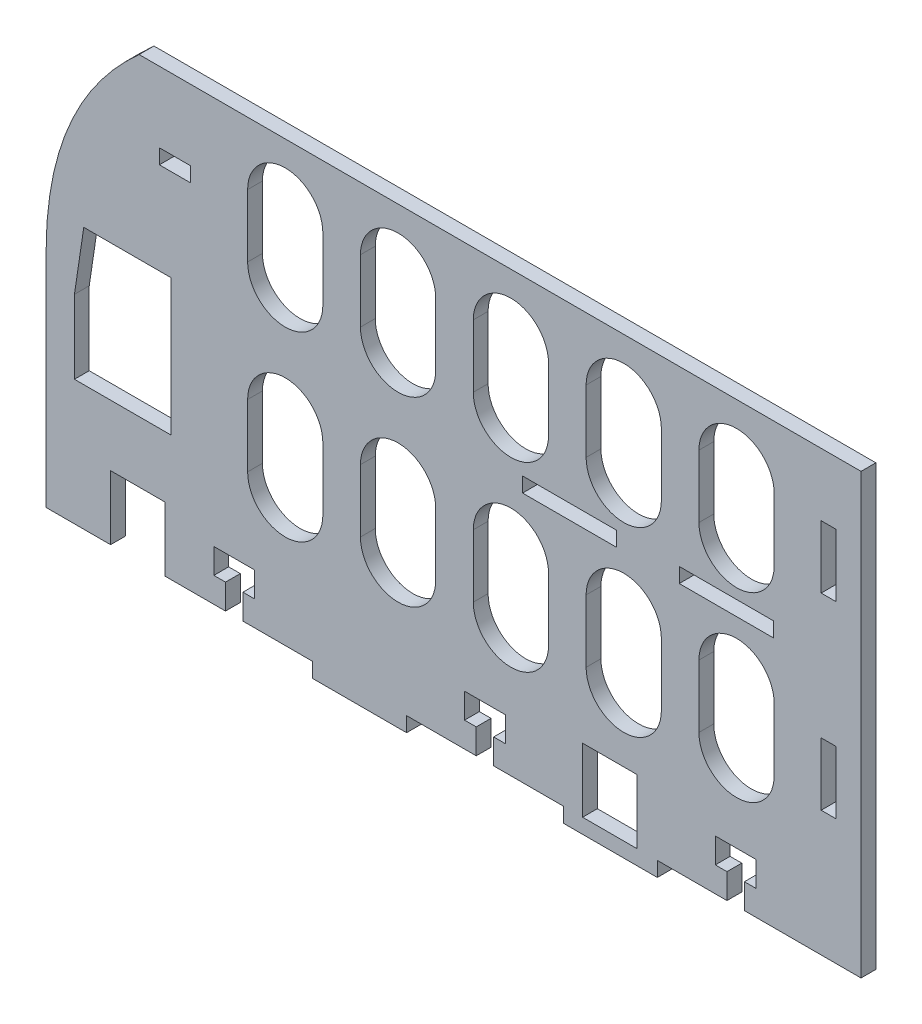
SolidWorks part; units mm, degrees
ref_plane "Front Plane" through (0, 0, 0) normal (0, 0, 1) x (1, 0, 0)
ref_plane "Top Plane" through (0, 0, 0) normal (0, 1, 0) x (1, 0, 0)
ref_plane "Right Plane" through (0, 0, 0) normal (1, 0, 0) x (0, 0, -1)
sketch "Sketch1" plane through (0, 0, 0) normal (0, 0, 1) x (1, 0, 0)
  line L0 (-76.2, -31.75) -> (-76.2, -10.2034) construction
  line L1 (2.72, 1.27) -> (-88.9648, 1.27) construction
  line L2 (50.8, 31.75) -> (50.8, -31.75)
  line L3 (-114.3, -31.75) -> (-101.25, -31.75)
  line L4 (25.58, 7.62) -> (25.58, -5.08) construction
  line L5 (-74.4347, -26.67) -> (-72.0725, -26.67)
  line L6 (-29.5275, -21.59) -> (-21.2725, -21.59)
  line L7 (-77.9653, -31.75) -> (-77.9653, -26.67)
  line L8 (-74.4347, -31.75) -> (-60.325, -31.75)
  line L9 (-74.4347, -31.75) -> (-74.4347, -26.67)
  line L10 (-80.3275, -26.67) -> (-77.9653, -26.67)
  line L11 (-80.3275, -26.67) -> (-80.3275, -21.59)
  line L12 (-80.3275, -21.59) -> (-72.0725, -21.59)
  line L13 (-72.0725, -26.67) -> (-72.0725, -21.59)
  line L14 (-21.2725, -26.67) -> (-21.2725, -21.59)
  line L15 (-23.6347, -26.67) -> (-21.2725, -26.67)
  line L16 (-29.5275, -26.67) -> (-27.1653, -26.67)
  line L17 (-27.1653, -31.75) -> (-27.1653, -26.67)
  line L18 (-23.6347, -31.75) -> (-23.6347, -26.67)
  line L19 (-29.5275, -26.67) -> (-29.5275, -21.59)
  line L20 (21.2725, -21.59) -> (29.5275, -21.59)
  line L21 (29.5275, -26.67) -> (29.5275, -21.59)
  line L22 (27.1653, -26.67) -> (29.5275, -26.67)
  line L23 (21.2725, -26.67) -> (23.6347, -26.67)
  line L24 (23.6347, -31.75) -> (23.6347, -26.67)
  line L25 (27.1653, -31.75) -> (27.1653, -26.67)
  line L26 (21.2725, -26.67) -> (21.2725, -21.59)
  line L27 (33.2, 7.62) -> (33.2, -5.08)
  line L28 (17.96, 7.62) -> (17.96, -5.08)
  line L29 (25.58, 1.27) -> (-66.1048, 1.27) construction
  line L30 (45.72, 31.75) -> (42.72, 31.75)
  line L31 (2.72, 7.62) -> (2.72, -5.08) construction
  line L32 (10.34, 7.62) -> (10.34, -5.08)
  line L33 (-4.9, 7.62) -> (-4.9, -5.08)
  line L34 (-23.6347, -31.75) -> (-9.525, -31.75)
  line L35 (27.1653, -31.75) -> (50.8, -31.75)
  line L36 (-114.3, -31.75) -> (-114.3, 12.7)
  line L37 (-20.14, 1.27) -> (-111.8248, 1.27) construction
  line L38 (-20.14, 7.62) -> (-20.14, -5.08) construction
  line L39 (-12.52, 7.62) -> (-12.52, -5.08)
  line L40 (45.72, -6.35) -> (42.72, -6.35)
  line L41 (45.72, 31.75) -> (45.72, 44.45)
  line L42 (9.525, -31.75) -> (23.6347, -31.75)
  line L43 (45.72, -6.35) -> (45.72, 6.35)
  line L44 (45.72, 6.35) -> (42.72, 6.35)
  line L45 (-60.325, -31.75) -> (-60.325, -34.75)
  line L46 (-60.325, -34.75) -> (-41.275, -34.75)
  line L47 (-41.275, -31.75) -> (-41.275, -34.75)
  line L48 (-50.8, -31.75) -> (-41.275, -34.75) construction
  line L49 (-60.325, -34.75) -> (-50.8, -31.75) construction
  line L50 (-41.275, -31.75) -> (-27.1653, -31.75)
  line L51 (-9.525, -31.75) -> (-9.525, -34.75)
  line L52 (-9.525, -34.75) -> (9.525, -34.75)
  line L53 (9.525, -31.75) -> (9.525, -34.75)
  line L54 (0, -31.75) -> (9.525, -34.75) construction
  line L55 (-9.525, -34.75) -> (0, -31.75) construction
  line L56 (42.72, -6.35) -> (42.72, 6.35)
  line L57 (45.72, 44.45) -> (42.72, 44.45)
  line L58 (42.72, 31.75) -> (42.72, 44.45)
  line L59 (-27.76, 7.62) -> (-27.76, -5.08)
  line L60 (-43, 1.27) -> (-134.6848, 1.27) construction
  line L61 (-43, 7.62) -> (-43, -5.08) construction
  line L62 (-35.38, 7.62) -> (-35.38, -5.08)
  line L63 (-95.4624, 57.15) -> (50.8, 57.15)
  line L64 (50.8, 57.15) -> (50.8, 31.75)
  line L65 (72.0725, -21.59) -> (80.3275, -21.59) [skipped]
  line L66 (80.3275, -26.67) -> (80.3275, -21.59) [skipped]
  line L67 (77.9653, -26.67) -> (80.3275, -26.67) [skipped]
  line L68 (72.0725, -26.67) -> (74.4347, -26.67) [skipped]
  line L69 (74.4347, -31.75) -> (74.4347, -26.67) [skipped]
  line L70 (77.9653, -31.75) -> (77.9653, -26.67) [skipped]
  line L71 (72.0725, -26.67) -> (72.0725, -21.59) [skipped]
  line L72 (-50.62, 7.62) -> (-50.62, -5.08)
  line L73 (-65.86, 1.27) -> (-157.5448, 1.27) construction
  line L74 (-65.86, 7.62) -> (-65.86, -5.08) construction
  line L75 (-58.24, 7.62) -> (-58.24, -5.08)
  line L76 (-73.48, 7.62) -> (-73.48, -5.08)
  line L77 (25.58, 38.1) -> (-65.86, 38.1) construction
  line L78 (25.58, 44.45) -> (25.58, 31.75) construction
  line L79 (33.2, 44.45) -> (33.2, 31.75)
  line L80 (17.96, 44.45) -> (17.96, 31.75)
  line L81 (2.72, 38.1) -> (-88.72, 38.1) construction
  line L82 (2.72, 44.45) -> (2.72, 31.75) construction
  line L83 (10.34, 44.45) -> (10.34, 31.75)
  line L84 (-4.9, 44.45) -> (-4.9, 31.75)
  line L85 (-20.14, 38.1) -> (-111.58, 38.1) construction
  line L86 (-20.14, 44.45) -> (-20.14, 31.75) construction
  line L87 (-12.52, 44.45) -> (-12.52, 31.75)
  line L88 (-27.76, 44.45) -> (-27.76, 31.75)
  line L89 (-43, 38.1) -> (-134.44, 38.1) construction
  line L90 (-43, 44.45) -> (-43, 31.75) construction
  line L91 (-35.38, 44.45) -> (-35.38, 31.75)
  line L92 (-50.62, 44.45) -> (-50.62, 31.75)
  line L93 (-65.86, 38.1) -> (-157.3, 38.1) construction
  line L94 (-65.86, 44.45) -> (-65.86, 31.75) construction
  line L95 (-58.24, 44.45) -> (-58.24, 31.75)
  line L96 (-73.48, 44.45) -> (-73.48, 31.75)
  line L97 (-88.72, 38.1) -> (-180.16, 38.1) construction
  line L98 (-108.5701, 2.1305) -> (-108.5701, 8.5217)
  line L99 (-91.3685, 42.8464) -> (-85.0185, 42.8464)
  line L100 (-91.3685, 42.8464) -> (-91.3685, 39.8464)
  line L101 (-108.5701, 8.5217) -> (-106.6773, 21.2269)
  line L102 (-106.6773, 21.2269) -> (-101.6751, 21.2269)
  line L103 (33.02, 22.0502) -> (33.02, 19.0502)
  line L104 (-91.3685, 39.8464) -> (-85.0185, 39.8464)
  line L105 (-85.0185, 42.8464) -> (-85.0185, 39.8464)
  line L106 (-91.3685, 42.8464) -> (-85.0185, 39.8464) construction
  line L107 (-91.3685, 39.8464) -> (-85.0185, 42.8464) construction
  line L108 (-88.9648, -6.3821) -> (-108.5701, -6.3821)
  line L109 (-88.9648, -6.3821) -> (-88.9648, 21.2269)
  line L110 (-88.9648, 21.2269) -> (-101.6751, 21.2269)
  line L111 (-108.5701, -6.3821) -> (-108.5701, 2.1305)
  line L112 (-17.78, 22.0502) -> (1.27, 22.0502)
  line L113 (13.97, 19.0502) -> (33.02, 19.0502)
  line L114 (-17.78, 19.0502) -> (1.27, 19.0502)
  line L115 (-90.25, -31.75) -> (-77.9653, -31.75)
  line L116 (13.97, 22.0502) -> (13.97, 19.0502)
  line L117 (-17.78, 22.0502) -> (-17.78, 19.0502)
  line L118 (1.27, 22.0502) -> (1.27, 19.0502)
  line L119 (13.97, 22.0502) -> (33.02, 22.0502)
  line L120 (-5.6133, -31.75) -> (-5.6133, -18.75)
  line L121 (-101.25, -31.75) -> (-101.25, -18.75)
  line L122 (-101.25, -18.75) -> (-90.25, -18.75)
  line L123 (-90.25, -31.75) -> (-90.25, -18.75)
  line L124 (-5.6133, -18.75) -> (5.3867, -18.75)
  line L125 (5.3867, -31.75) -> (5.3867, -18.75)
  line L126 (-5.6133, -31.75) -> (5.3867, -31.75)
  line L166 (-88.72, 44.45) -> (-88.72, 31.75) construction
  line L167 (-81.1, 44.45) -> (-81.1, 31.75) [skipped]
  line L168 (-96.34, 44.45) -> (-96.34, 31.75) [skipped]
  line L169 (-88.72, 44.45) -> (-88.72, 31.75) construction
  line L170 (-81.1, 44.45) -> (-81.1, 31.75) [skipped]
  line L171 (-96.34, 44.45) -> (-96.34, 31.75) [skipped]
  arc A0 (10.34, 7.62) -> (-4.9, 7.62) centre (2.72, 7.62) ccw
  arc A1 (33.2, 7.62) -> (17.96, 7.62) centre (25.58, 7.62) ccw
  arc A2 (17.96, -5.08) -> (33.2, -5.08) centre (25.58, -5.08) ccw
  arc A3 (-4.9, -5.08) -> (10.34, -5.08) centre (2.72, -5.08) ccw
  arc A4 (-12.52, 7.62) -> (-27.76, 7.62) centre (-20.14, 7.62) ccw
  arc A5 (-27.76, -5.08) -> (-12.52, -5.08) centre (-20.14, -5.08) ccw
  arc A6 (-35.38, 7.62) -> (-50.62, 7.62) centre (-43, 7.62) ccw
  arc A7 (-50.62, -5.08) -> (-35.38, -5.08) centre (-43, -5.08) ccw
  arc A8 (-58.24, 7.62) -> (-73.48, 7.62) centre (-65.86, 7.62) ccw
  arc A9 (-73.48, -5.08) -> (-58.24, -5.08) centre (-65.86, -5.08) ccw
  arc A10 (33.2, 44.45) -> (17.96, 44.45) centre (25.58, 44.45) ccw
  arc A11 (17.96, 31.75) -> (33.2, 31.75) centre (25.58, 31.75) ccw
  arc A12 (10.34, 44.45) -> (-4.9, 44.45) centre (2.72, 44.45) ccw
  arc A13 (-4.9, 31.75) -> (10.34, 31.75) centre (2.72, 31.75) ccw
  arc A14 (-12.52, 44.45) -> (-27.76, 44.45) centre (-20.14, 44.45) ccw
  arc A15 (-27.76, 31.75) -> (-12.52, 31.75) centre (-20.14, 31.75) ccw
  arc A16 (-35.38, 44.45) -> (-50.62, 44.45) centre (-43, 44.45) ccw
  arc A17 (-50.62, 31.75) -> (-35.38, 31.75) centre (-43, 31.75) ccw
  arc A18 (-58.24, 44.45) -> (-73.48, 44.45) centre (-65.86, 44.45) ccw
  arc A19 (-73.48, 31.75) -> (-58.24, 31.75) centre (-65.86, 31.75) ccw
  arc A62 (-81.1, 44.45) -> (-96.34, 44.45) centre (-88.72, 44.45) ccw [skipped]
  arc A63 (-96.34, 31.75) -> (-81.1, 31.75) centre (-88.72, 31.75) ccw [skipped]
  spline S0 degree 2 poles (-114.3, 12.7) (-114.4464, 40.173) (-95.4624, 57.15) knots 0 0 0 1 1 1
  point P3 (25.58, 1.27)
  point P44 (2.72, 1.27)
  point P49 (-50.8, -31.75)
  point P56 (0, -31.75)
  point P65 (-20.14, 1.27)
  point P98 (-43, 1.27)
  point P101 (-88.1935, 41.3464)
  point P108 (-65.86, 1.27)
  point P117 (25.58, 38.1)
  point P127 (2.72, 38.1)
  point P136 (-20.14, 38.1)
  point P145 (-43, 38.1)
  point P154 (-65.86, 38.1)
  point P169 (-88.72, 38.1)
  point P183 (-88.72, 38.1)
  point P190 (-88.72, 38.1)
  point P197 (-88.72, 38.1)
  point P204 (-88.72, 38.1)
  point P211 (-88.72, 38.1)
  point P218 (-88.72, 38.1)
  point P225 (-88.72, 38.1)
  point P232 (-88.72, 38.1)
  point P239 (-88.72, 38.1)
  point P246 (-88.72, 38.1)
  point P253 (-88.72, 38.1)
  point P260 (-88.72, 38.1)
  point P267 (-88.72, 38.1)
  point P274 (-88.72, 38.1)
  point P281 (-88.72, 38.1)
  point P288 (-88.72, 38.1)
  point P295 (-88.72, 38.1)
  point P302 (-88.72, 38.1)
  point P309 (-88.72, 38.1)
  point P316 (-88.72, 38.1)
  dimension "D14" = 7.62
  dimension "D15" = 12.7
  dimension "D13" = 12.7
  dimension "D22" = 25.4
  dimension "D27" = 7.62
  dimension "D2" = 25.4
  dimension "D3" = 165.1
  dimension "D4" = 5
  dimension "D5" = 3
  dimension "D6" = 5.08
  dimension "D7" = 5.08
  dimension "D8" = 3.5306
  dimension "D9" = 1.7653
  dimension "D10" = 8.255
  dimension "D11" = 4.1275
  dimension "D16" = 3
  dimension "D17" = 3
  dimension "D18" = 19.05
  dimension "D19" = 19.05
  dimension "D20" = 5.08
  dimension "D21" = 12.7
  dimension "D23" = 88.9
  dimension "D24" = 33.02
  dimension "D25" = 69.85
  dimension "D26" = 12.7
  dimension "D29" = 3
  dimension "D30" = 6.35
  dimension "D31" = 3
  dimension "D32" = 11
  dimension "D33" = 13
  dimension "D34" = 19.05
  dimension "D35" = 12.7
  dimension "D36" = 19.05
  dimension "D37" = 13.05
  dimension "D38" = 13
  dimension "D39" = 11
  dimension "D12" = 4
  dimension "D28" = 6
extrude "Boss-Extrude1" add sketch "Sketch1" along normal blind 3
